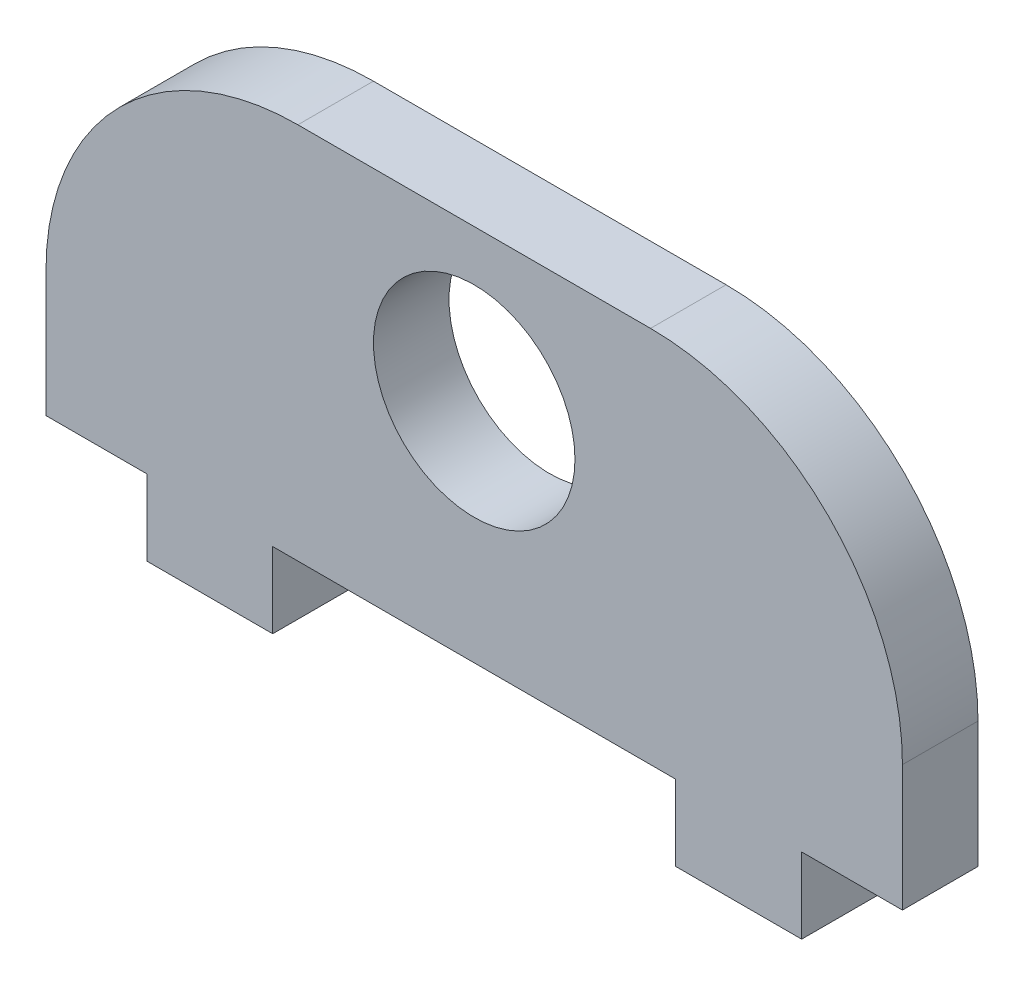
SolidWorks part; units mm, degrees
ref_plane "Front Plane" through (0, 0, 0) normal (0, 0, 1) x (1, 0, 0)
ref_plane "Top Plane" through (0, 0, 0) normal (0, 1, 0) x (1, 0, 0)
ref_plane "Right Plane" through (0, 0, 0) normal (1, 0, 0) x (0, 0, -1)
sketch "Sketch1" plane through (0, 0, 0) normal (0, 0, 1) x (1, 0, 0)
  line L0 (0, 7.5) -> (0, -12.5) construction
  line L1 (-17, -7.5) -> (-13, -7.5)
  line L2 (-17, -7.5) -> (-17, 7.5)
  line L3 (-17, 7.5) -> (17, 7.5)
  line L4 (17, -7.5) -> (17, 7.5)
  line L5 (-17, -7.5) -> (17, 7.5) construction
  line L6 (-17, 7.5) -> (17, -7.5) construction
  line L7 (0, -12.5) -> (8, -7.5) construction
  line L8 (17, 0) -> (-17, 0) construction
  line L9 (8, -7.5) -> (8, -10.5) construction
  line L10 (8, -10.5) -> (13, -10.5) construction
  line L11 (13, -10.5) -> (13, -7.5) construction
  line L12 (8, -7.5) -> (8, -10.5)
  line L13 (8, -10.5) -> (13, -10.5)
  line L14 (13, -10.5) -> (13, -7.5)
  line L15 (13, -7.5) -> (17, -7.5)
  line L16 (-13, -10.5) -> (-13, -7.5)
  line L17 (-8, -10.5) -> (-13, -10.5)
  line L18 (-8, -7.5) -> (-8, -10.5)
  line L19 (-8, -7.5) -> (8, -7.5)
  circle A2 centre (0, 1.5) radius 4
  point P0 (0, 0)
  dimension "D6" = 8
  dimension "D1" = 34
  dimension "D2" = 15
  dimension "D3" = 3
  dimension "D4" = 5
  dimension "D5" = 8
  dimension "D7" = 6
extrude "Boss-Extrude1" add sketch "Sketch1" along normal blind 3
fillet "Fillet1" radius 10 2 edges at (-17, 7.5, 1.5) (17, 7.5, 1.5)
